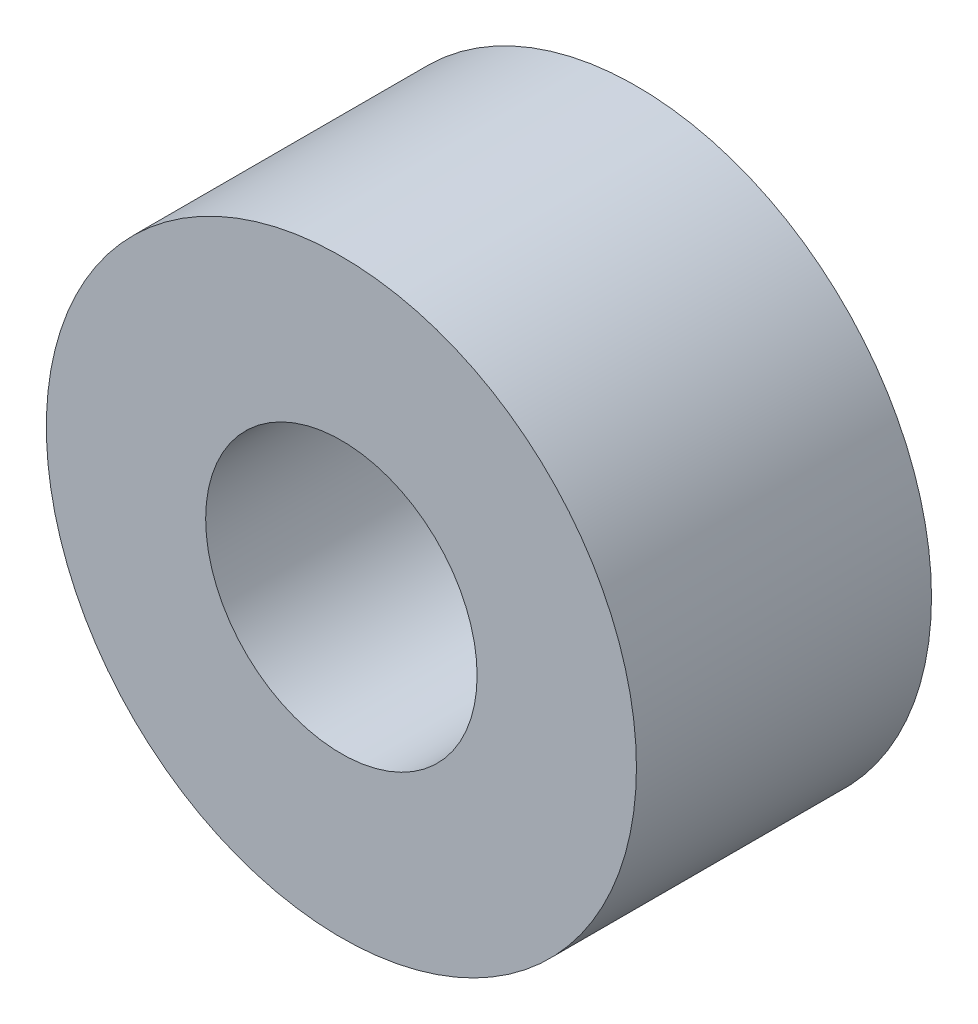
SolidWorks part; units mm, degrees
material "Nylon 101"
ref_plane "Front Plane" through (0, 0, 0) normal (0, 0, 1) x (1, 0, 0)
ref_plane "Top Plane" through (0, 0, 0) normal (0, 1, 0) x (1, 0, 0)
ref_plane "Right Plane" through (0, 0, 0) normal (1, 0, 0) x (0, 0, -1)
sketch "Sketch1" plane through (0, 0, 0) normal (0, 0, 1) x (1, 0, 0)
  circle A0 centre (0, 0) radius 3.175
  circle A1 centre (0, 0) radius 1.4605
  dimension "OD" = 6.35
  dimension "ID" = 2.921
extrude "Extrude1" add sketch "Sketch1" along normal mid plane 3.175
sketch "Sketch2" plane through (0, 0, 0) normal (1, 0, 0) x (0, 0, -1)
  line L0 (-1.5875, -1.4605) -> (1.5875, -1.4605) construction
  line L3 (1.5875, 1.4605) -> (-1.5875, 1.4605) construction
  line L5 (-1.5875, -1.4605) -> (1.5875, -1.4605)
  line L6 (1.5875, 1.4605) -> (-1.5875, 1.4605)
sketch "Sketch4" plane through (0, 0, 1.5875) normal (0, 0, 1) x (1, 0, 0)
  line L0 (0, 0) -> (-1.0327, 1.0327)
  line L1 (0, -1.7463) -> (0, 1.7463) construction
  circle A0 centre (0, 0) radius 1.4605 construction
  dimension "D1" = 45
